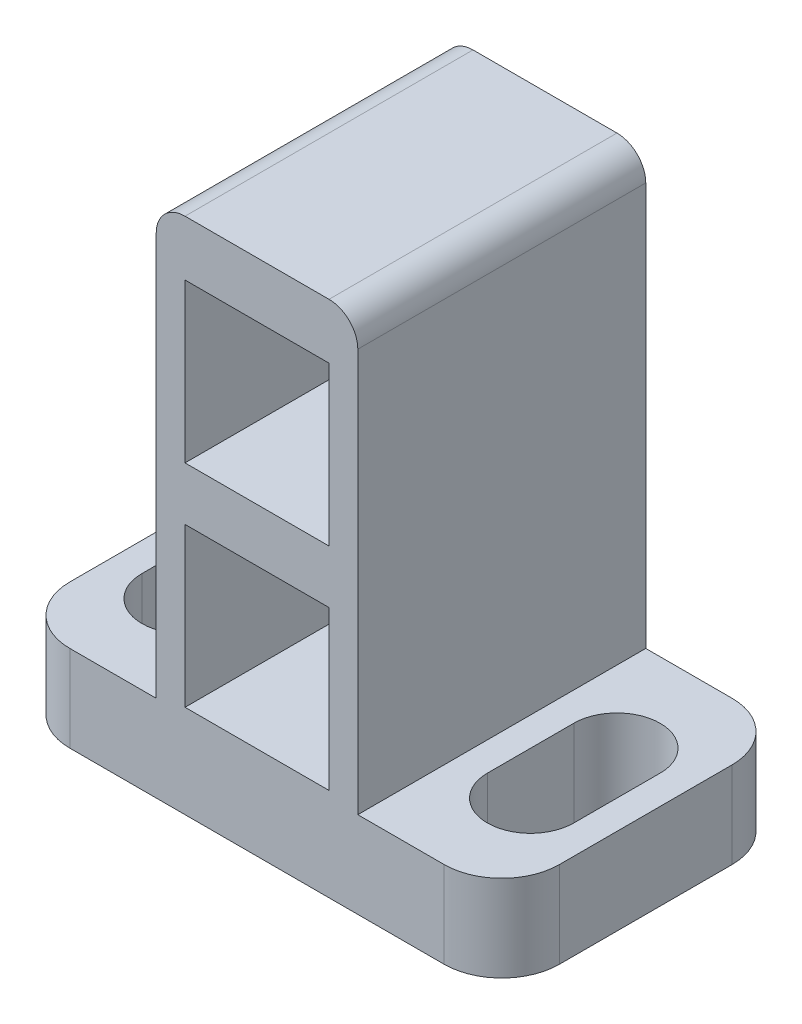
SolidWorks part; units mm, degrees
ref_plane "Front Plane" through (0, 0, 0) normal (0, 0, 1) x (1, 0, 0)
ref_plane "Top Plane" through (0, 0, 0) normal (0, 1, 0) x (1, 0, 0)
ref_plane "Right Plane" through (0, 0, 0) normal (1, 0, 0) x (0, 0, -1)
sketch "Sketch1" plane through (0, 0, 0) normal (0, 0, 1) x (1, 0, 0)
  line L1 (-3.5, -9) -> (3.5, -9)
  line L2 (-3.5, -9) -> (-3.5, 9)
  line L3 (-3.5, 9) -> (3.5, 9)
  line L4 (3.5, -9) -> (3.5, 9)
  line L5 (-3.5, -9) -> (3.5, 9) construction
  line L6 (-3.5, 9) -> (3.5, -9) construction
  point P0 (0, 0)
  dimension "D1" = 7
  dimension "D2" = 18
extrude "Boss-Extrude1" add sketch "Sketch1" along normal blind 8
sketch "Sketch3" plane through (0, 0, 0) normal (0, 0, -1) x (-1, 0, 0)
  line L1 (3.5, 9) -> (-3.5, 9)
  line L2 (3.5, 9) -> (3.5, -9)
  line L3 (3.5, -9) -> (-3.5, -9)
  line L4 (-3.5, 9) -> (-3.5, -9)
extrude "Boss-Extrude2" add sketch "Sketch3" along normal blind 2
sketch "Sketch2" plane through (0, 0, 8) normal (0, 0, 1) x (1, 0, 0)
  line L1 (-2.5, 1.58) -> (2.5, 1.58)
  line L2 (-2.5, 1.58) -> (-2.5, 7.08)
  line L3 (-2.5, 7.08) -> (2.5, 7.08)
  line L4 (2.5, 1.58) -> (2.5, 7.08)
  line L5 (-2.5, 1.58) -> (2.5, 7.08) construction
  line L6 (-2.5, 7.08) -> (2.5, 1.58) construction
  line L7 (-2.5, -5.77) -> (2.5, -5.77)
  line L8 (-2.5, -5.77) -> (-2.5, -0.27)
  line L9 (-2.5, -0.27) -> (2.5, -0.27)
  line L10 (2.5, -5.77) -> (2.5, -0.27)
  line L11 (-2.5, -5.77) -> (2.5, -0.27) construction
  line L12 (-2.5, -0.27) -> (2.5, -5.77) construction
  line L19 (0, 9) -> (0, -9) construction
  line L20 (3.5, 9) -> (-3.5, 9) construction
  line L21 (-3.5, -9) -> (3.5, -9) construction
  point P0 (0, 4.33)
  point P5 (0, -3.02)
  dimension "D1" = 5.5
  dimension "D2" = 16.08
  dimension "D3" = 5
  dimension "D4" = 1.85
extrude "Cut-Extrude1" cut sketch "Sketch2" against normal offset from surface (8 mm away) 2 up to face at (0, 0, -2)
sketch "Sketch4" plane through (0, 0, 0) normal (0, 0, 1) x (1, 0, 0)
  line L0 (2.5, 7.08) -> (-2.5, 7.08) construction
  line L1 (-2.5, 1.58) -> (2.5, 1.58) construction
  line L2 (-2.5, 1.58) -> (-2.5, 7.08) construction
  line L3 (-2.5, 7.08) -> (2.5, 7.08) construction
  line L4 (2.5, 1.58) -> (2.5, 7.08) construction
  line L5 (-2.5, 1.58) -> (2.5, 7.08) construction
  line L6 (-2.5, 7.08) -> (2.5, 1.58) construction
  line L7 (2.5, 1.58) -> (2.5, 7.08) construction
  line L8 (-2.5, -0.27) -> (2.5, -5.77) construction
  line L9 (-2.5, 7.08) -> (-2.5, 1.58) construction
  line L10 (-2.5, 1.58) -> (2.5, 1.58) construction
  circle A0 centre (0, 4.33) radius 1
  circle A1 centre (0, -3.02) radius 1
  dimension "D1" = 2
extrude "Cut-Extrude2" cut sketch "Sketch4" against normal through all
sketch "Sketch5" plane through (0, -9, 0) normal (0, -1, 0) x (1, 0, 0)
  line L0 (3.5, -2) -> (-3.5, -2) construction
  line L1 (3.5, 8) -> (8.5, 8)
  line L2 (3.5, 8) -> (3.5, -2)
  line L3 (3.5, -2) -> (8.5, -2)
  line L4 (8.5, 8) -> (8.5, -2)
  line L5 (6, 4.5) -> (6, 1.5) construction
  line L6 (7.5, 4.5) -> (7.5, 1.5)
  line L7 (4.5, 4.5) -> (4.5, 1.5)
  line L8 (3.5, 3) -> (8.5, 3) construction
  line L11 (6, -2) -> (6, 8) construction
  arc A0 (7.5, 4.5) -> (4.5, 4.5) centre (6, 4.5) ccw
  arc A1 (4.5, 1.5) -> (7.5, 1.5) centre (6, 1.5) ccw
  point P9 (6, 3)
  dimension "D1" = 5
  dimension "D2" = 3
  dimension "D3" = 3
extrude "Boss-Extrude3" add sketch "Sketch5" against normal blind 3
fillet "Fillet1" radius 2 2 edges at (8.5, -7.5, -2) (8.5, -7.5, 8)
mirror "Mirror2" about plane through (0, 0, 0) normal (1, 0, 0) of "Fillet1", "Boss-Extrude3"
fillet "Fillet2" radius 1 2 edges at (3.5, 9, 3) (-3.5, 9, 3)
